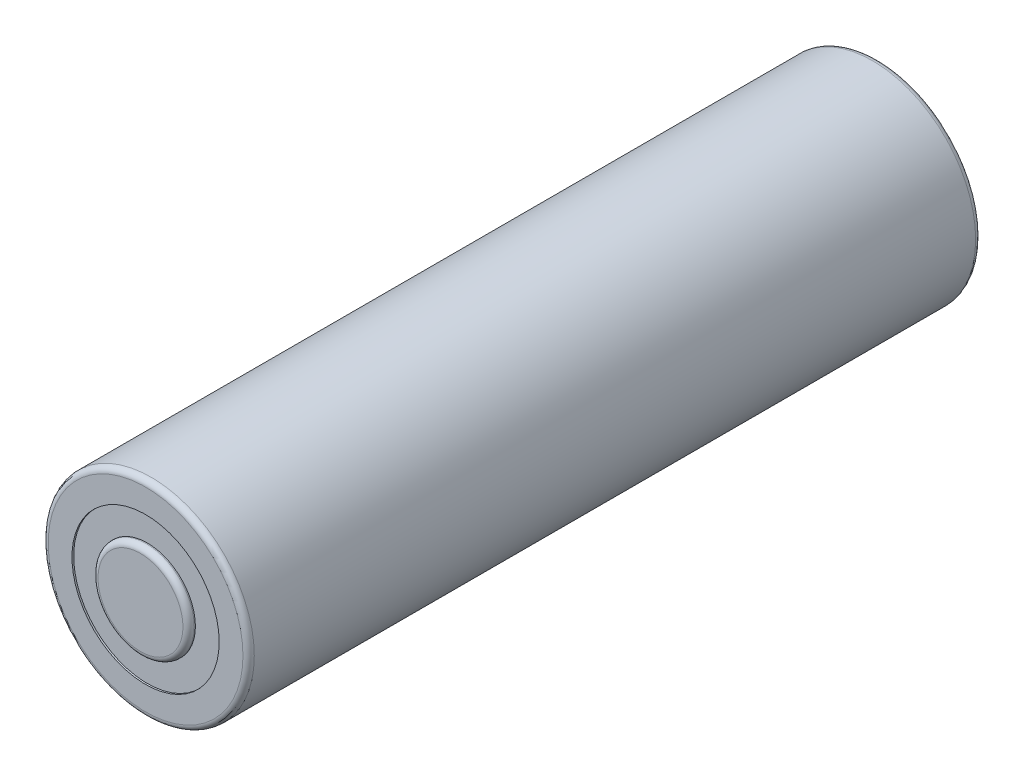
SolidWorks part; units mm, degrees
ref_plane "前视基准面" through (0, 0, 0) normal (0, 0, 1) x (1, 0, 0)
ref_plane "上视基准面" through (0, 0, 0) normal (0, 1, 0) x (1, 0, 0)
ref_plane "右视基准面" through (0, 0, 0) normal (1, 0, 0) x (0, 0, -1)
sketch "草图1" plane through (0, 0, 0) normal (0, 0, 1) x (1, 0, 0)
  circle A0 centre (-28.8744, 15.272) radius 9.1
  dimension "D1" = 18.2
extrude "凸台-拉伸1" add sketch "草图1" along normal blind 64.7
fillet "圆角1" radius 0.5 1 edges at (-19.7744, 15.272, 0)
fillet "圆角2" radius 0.5 1 edges at (-19.7744, 15.272, 64.7)
sketch "草图2" plane through (0, 0, 0) normal (0, 0, -1) x (-1, 0, 0)
  circle A0 centre (28.8744, 15.272) radius 6.5
  dimension "D1" = 13
extrude "切除-拉伸1" cut sketch "草图2" against normal blind 0.35
sketch "草图3" plane through (0, 0, 64.7) normal (0, 0, 1) x (1, 0, 0)
  circle A0 centre (-28.8744, 15.272) radius 6.5
  dimension "D1" = 13
extrude "切除-拉伸2" cut sketch "草图3" against normal blind 0.35
sketch "草图4" plane through (0, 0, 64.35) normal (0, 0, 1) x (1, 0, 0)
  circle A0 centre (-28.8744, 15.272) radius 4.25
  dimension "D1" = 8.5
extrude "凸台-拉伸2" add sketch "草图4" along normal blind 0.8
fillet "圆角3" radius 0.5 1 edges at (-24.6244, 15.272, 65.15)
sketch "草图5" plane through (0, 0, 64.35) normal (0, 0, 1) x (1, 0, 0)
  circle A0 centre (-28.8744, 15.272) radius 6.5
  circle A1 centre (-28.8744, 15.272) radius 4.25
extrude "凸台-拉伸3" add sketch "草图5" along normal blind 0.2
